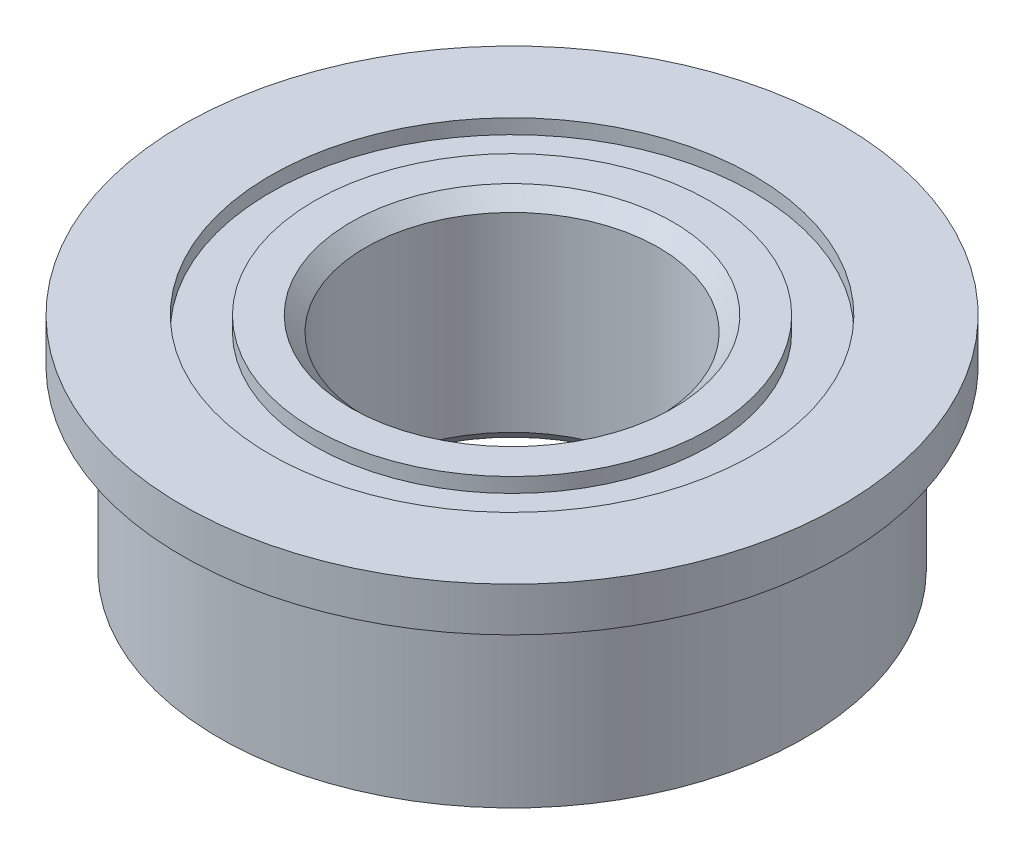
SolidWorks part; units mm, degrees
material "Plain Carbon Steel"
ref_plane "Front Plane" through (0, 0, 0) normal (0, 0, 1) x (1, 0, 0)
ref_plane "Top Plane" through (0, 0, 0) normal (0, 1, 0) x (1, 0, 0)
ref_plane "Right Plane" through (0, 0, 0) normal (1, 0, 0) x (0, 0, -1)
sketch "Sketch1" plane through (0, 0, 0) normal (0, 0, 1) x (1, 0, 0)
  line L0 (0, 0) -> (0, 3.2117) construction
  line L1 (0, 0) -> (2, 0) construction
  line L2 (2, -2.4) -> (2, 0.6)
  line L3 (2, -2.4) -> (2.7, -2.4)
  line L4 (2.7, -2.4) -> (2.7, -2.2)
  line L5 (2.7, -2.2) -> (3.3, -2.2)
  line L6 (3.3, -2.2) -> (3.3, -2.4)
  line L7 (3.3, -2.4) -> (4, -2.4)
  line L8 (4, -2.4) -> (4, 0)
  line L9 (4.5, 0.6) -> (3.3, 0.6)
  line L10 (3.3, 0.6) -> (3.3, 0.4)
  line L11 (3.3, 0.4) -> (2.7, 0.4)
  line L12 (2, 0.6) -> (2.7, 0.6)
  line L13 (4, 0) -> (4.5, 0)
  line L14 (4.5, 0) -> (4.5, 0.6)
  line L15 (2.7, 0.6) -> (2.7, 0.4)
  line L16 (3, -3.1894) -> (3, 1.3808) construction
  dimension "D1" = 0.2
  dimension "D2" = 4
  dimension "D3" = 8
  dimension "D4" = 5.4
  dimension "D5" = 0.6
  dimension "D6" = 9
  dimension "D7" = 3
revolve "Revolve1" add sketch "Sketch1" angle 360 about L0
chamfer "Chamfer1" distance 0.2 angle 45 2 edges at (0, 0.6, -2) (0, -2.4, -2)
